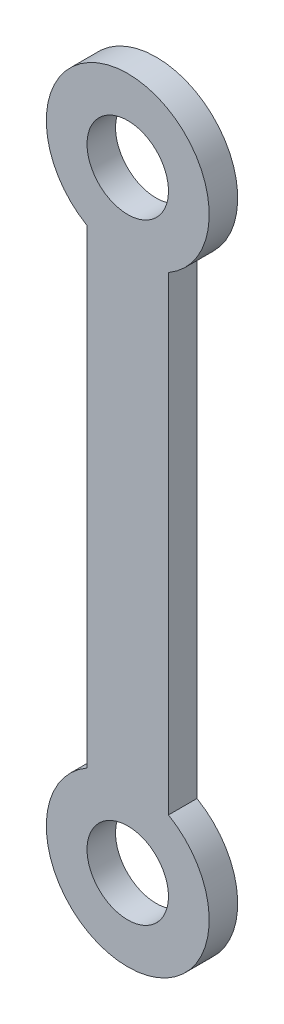
SolidWorks part; units mm, degrees
ref_plane "Front Plane" through (0, 0, 0) normal (0, 0, 1) x (1, 0, 0)
ref_plane "Top Plane" through (0, 0, 0) normal (0, 1, 0) x (1, 0, 0)
ref_plane "Right Plane" through (0, 0, 0) normal (1, 0, 0) x (0, 0, -1)
sketch "Sketch1" plane through (0, 0, 0) normal (0, 0, 1) x (1, 0, 0)
  line L0 (36.798, 101.1427) -> (103.7813, 99.6461) construction
  line L1 (0, 0) -> (0, 15) construction
  line L2 (0, 15) -> (-2, 15) construction
  line L3 (-2, 26.5359) -> (-2, 3.4641)
  line L4 (2, 26.5359) -> (2, 3.4641)
  circle A0 centre (0, 0) radius 4 construction
  circle A1 centre (0, 0) radius 2
  arc A2 (2, 3.4641) -> (-2, 3.4641) centre (0, 0) cw
  circle A3 centre (0, 30) radius 2
  arc A4 (2, 26.5359) -> (-2, 26.5359) centre (0, 30) ccw
  point P17 (2, 15)
  dimension "D2" = 4
  dimension "D3" = 2
  dimension "D1" = 67
  dimension "D4" = 4
  dimension "D5" = 15
extrude "Boss-Extrude1" add sketch "Sketch1" along normal blind 1.4
